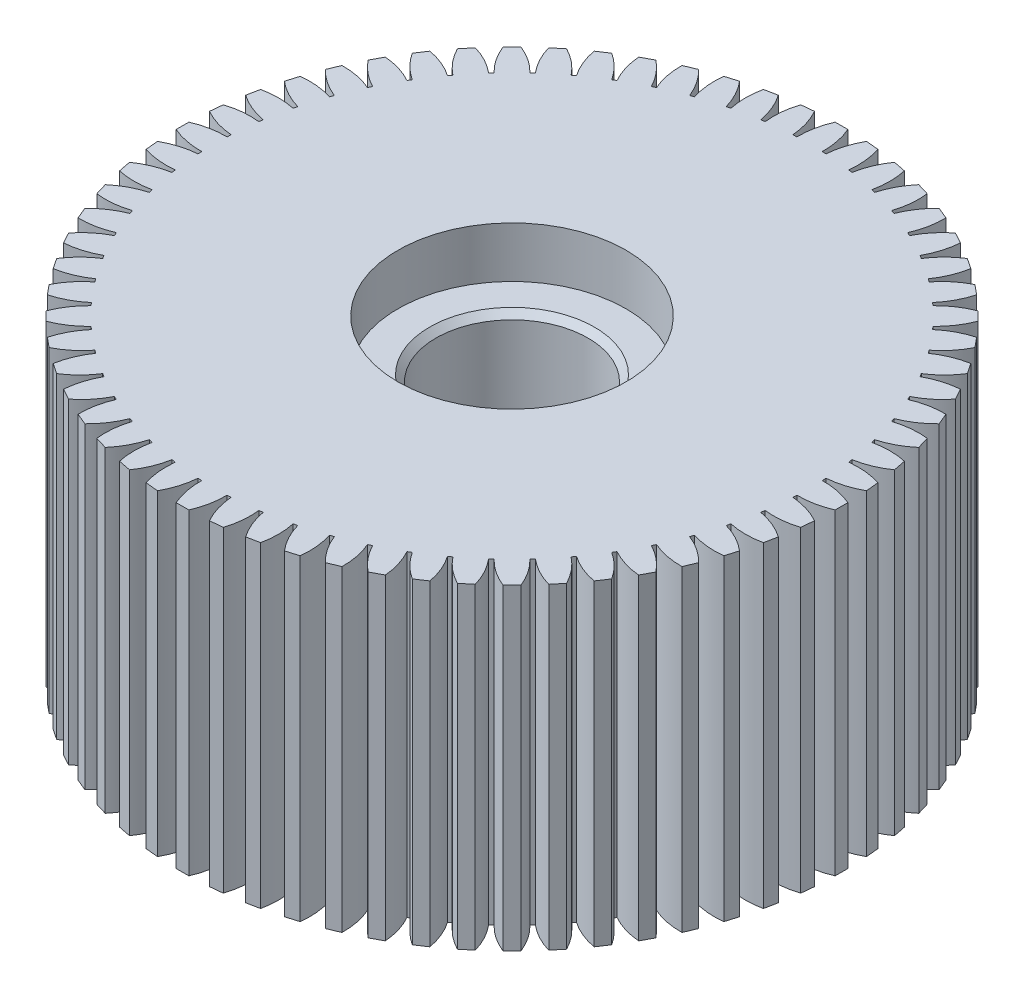
SolidWorks part; units mm, degrees
ref_plane "Front Plane" through (0, 0, 0) normal (0, 0, 1) x (1, 0, 0)
ref_plane "Top Plane" through (0, 0, 0) normal (0, 1, 0) x (1, 0, 0)
ref_plane "Right Plane" through (0, 0, 0) normal (1, 0, 0) x (0, 0, -1)
sketch "Sketch2" plane through (0, 0, 0) normal (0, 1, 0) x (1, 0, 0)
  circle A0 centre (0, 0) radius 23.5
  dimension "D1" = 47
extrude "Boss-Extrude1" add sketch "Sketch2" along normal blind 25
sketch "Sketch3" plane through (0, 25, 0) normal (0, 1, 0) x (1, 0, 0)
  line L0 (0, 0) -> (0, 28.1203) construction
  line L1 (-0.5, 25.9952) -> (0.5, 25.9952)
  line L2 (2.0504, 25.919) -> (3.0456, 25.821)
  line L3 (4.581, 25.5932) -> (5.5618, 25.3982)
  line L4 (7.0675, 25.021) -> (8.0245, 24.7307)
  line L5 (9.486, 24.2078) -> (10.4099, 23.8251)
  line L6 (11.8131, 23.1614) -> (12.695, 22.69)
  line L7 (14.0264, 21.892) -> (14.8579, 21.3364)
  line L8 (16.1047, 20.4118) -> (16.8777, 19.7774)
  line L9 (18.0278, 18.7349) -> (18.7349, 18.0278)
  line L10 (19.7774, 16.8777) -> (20.4118, 16.1047)
  line L11 (21.3364, 14.8579) -> (21.892, 14.0264)
  line L12 (22.69, 12.695) -> (23.1614, 11.8131)
  line L13 (23.8251, 10.4099) -> (24.2078, 9.486)
  line L14 (24.7307, 8.0245) -> (25.021, 7.0675)
  line L15 (25.3982, 5.5618) -> (25.5932, 4.581)
  line L16 (25.821, 3.0456) -> (25.919, 2.0504)
  line L17 (25.9952, 0.5) -> (25.9952, -0.5)
  line L18 (25.919, -2.0504) -> (25.821, -3.0456)
  line L19 (25.5932, -4.581) -> (25.3982, -5.5618)
  line L20 (25.021, -7.0675) -> (24.7307, -8.0245)
  line L21 (24.2078, -9.486) -> (23.8251, -10.4099)
  line L22 (23.1614, -11.8131) -> (22.69, -12.695)
  line L23 (21.892, -14.0264) -> (21.3364, -14.8579)
  line L24 (20.4118, -16.1047) -> (19.7774, -16.8777)
  line L25 (18.7349, -18.0278) -> (18.0278, -18.7349)
  line L26 (16.8777, -19.7774) -> (16.1047, -20.4118)
  line L27 (14.8579, -21.3364) -> (14.0264, -21.892)
  line L28 (12.695, -22.69) -> (11.8131, -23.1614)
  line L29 (10.4099, -23.8251) -> (9.486, -24.2078)
  line L30 (8.0245, -24.7307) -> (7.0675, -25.021)
  line L31 (5.5618, -25.3982) -> (4.581, -25.5932)
  line L32 (3.0456, -25.821) -> (2.0504, -25.919)
  line L33 (0.5, -25.9952) -> (-0.5, -25.9952)
  line L34 (-2.0504, -25.919) -> (-3.0456, -25.821)
  line L35 (-4.581, -25.5932) -> (-5.5618, -25.3982)
  line L36 (-7.0675, -25.021) -> (-8.0245, -24.7307)
  line L37 (-9.486, -24.2078) -> (-10.4099, -23.8251)
  line L38 (-11.8131, -23.1614) -> (-12.695, -22.69)
  line L39 (-14.0264, -21.892) -> (-14.8579, -21.3364)
  line L40 (-16.1047, -20.4118) -> (-16.8777, -19.7774)
  line L41 (-18.0278, -18.7349) -> (-18.7349, -18.0278)
  line L42 (-19.7774, -16.8777) -> (-20.4118, -16.1047)
  line L43 (-21.3364, -14.8579) -> (-21.892, -14.0264)
  line L44 (-22.69, -12.695) -> (-23.1614, -11.8131)
  line L45 (-23.8251, -10.4099) -> (-24.2078, -9.486)
  line L46 (-24.7307, -8.0245) -> (-25.021, -7.0675)
  line L47 (-25.3982, -5.5618) -> (-25.5932, -4.581)
  line L48 (-25.821, -3.0456) -> (-25.919, -2.0504)
  line L49 (-25.9952, -0.5) -> (-25.9952, 0.5)
  line L50 (-25.919, 2.0504) -> (-25.821, 3.0456)
  line L51 (-25.5932, 4.581) -> (-25.3982, 5.5618)
  line L52 (-25.021, 7.0675) -> (-24.7307, 8.0245)
  line L53 (-24.2078, 9.486) -> (-23.8251, 10.4099)
  line L54 (-23.1614, 11.8131) -> (-22.69, 12.695)
  line L55 (-21.892, 14.0264) -> (-21.3364, 14.8579)
  line L56 (-20.4118, 16.1047) -> (-19.7774, 16.8777)
  line L57 (-18.7349, 18.0278) -> (-18.0278, 18.7349)
  line L58 (-16.8777, 19.7774) -> (-16.1047, 20.4118)
  line L59 (-14.8579, 21.3364) -> (-14.0264, 21.892)
  line L60 (-12.695, 22.69) -> (-11.8131, 23.1614)
  line L61 (-10.4099, 23.8251) -> (-9.486, 24.2078)
  line L62 (-8.0245, 24.7307) -> (-7.0675, 25.021)
  line L63 (-5.5618, 25.3982) -> (-4.581, 25.5932)
  line L64 (-3.0456, 25.821) -> (-2.0504, 25.919)
  circle A0 centre (0, 0) radius 26
  circle A1 centre (0, 0) radius 23.5 construction
  circle A2 centre (0, 0) radius 23.5
  arc A3 (-1, 23.4787) -> (-0.5, 25.9952) centre (4.9989, 23.5947) cw
  arc A4 (1, 23.4787) -> (0.5, 25.9952) centre (-4.9989, 23.5947) ccw
  arc A5 (1.3061, 23.4637) -> (2.0504, 25.919) centre (7.2875, 22.9911) cw
  arc A6 (3.2965, 23.2676) -> (3.0456, 25.821) centre (-2.6621, 23.9711) ccw
  arc A7 (3.5997, 23.2227) -> (4.581, 25.5932) centre (9.5059, 22.1661) cw
  arc A8 (5.5613, 22.8325) -> (5.5618, 25.3982) centre (-0.2997, 24.1166) ccw
  arc A9 (5.8586, 22.758) -> (7.0675, 25.021) centre (11.6328, 21.1276) cw
  arc A10 (7.7725, 22.1774) -> (8.0245, 24.7307) centre (2.0656, 24.0298) ccw
  arc A11 (8.061, 22.0742) -> (9.486, 24.2078) centre (13.6477, 19.8857) cw
  arc A12 (9.9088, 21.3088) -> (10.4099, 23.8251) centre (4.4109, 23.7117) ccw
  arc A13 (10.1859, 21.1778) -> (11.8131, 23.1614) centre (15.5311, 18.4522) cw
  arc A14 (11.9497, 20.235) -> (12.695, 22.69) centre (6.7138, 23.1651) ccw
  arc A15 (12.2126, 20.0774) -> (14.0264, 21.892) centre (17.2649, 16.8411) cw
  arc A16 (13.8755, 18.9663) -> (14.8579, 21.3364) centre (8.9521, 22.3955) ccw
  arc A17 (14.1217, 18.7837) -> (16.1047, 20.4118) centre (18.8325, 15.0677) cw
  arc A18 (15.6677, 17.5149) -> (16.8777, 19.7774) centre (11.1041, 21.4102) ccw
  arc A19 (15.8949, 17.3091) -> (18.0278, 18.7349) centre (20.2187, 13.1492) cw
  arc A20 (17.3091, 15.8949) -> (18.7349, 18.0278) centre (13.1492, 20.2187) ccw
  arc A21 (17.5149, 15.6677) -> (19.7774, 16.8777) centre (21.4102, 11.1041) cw
  arc A22 (18.7837, 14.1217) -> (20.4118, 16.1047) centre (15.0677, 18.8325) ccw
  arc A23 (18.9663, 13.8755) -> (21.3364, 14.8579) centre (22.3955, 8.9521) cw
  arc A24 (20.0774, 12.2126) -> (21.892, 14.0264) centre (16.8411, 17.2649) ccw
  arc A25 (20.235, 11.9497) -> (22.69, 12.695) centre (23.1651, 6.7138) cw
  arc A26 (21.1778, 10.1859) -> (23.1614, 11.8131) centre (18.4522, 15.5311) ccw
  arc A27 (21.3088, 9.9088) -> (23.8251, 10.4099) centre (23.7117, 4.4109) cw
  arc A28 (22.0742, 8.061) -> (24.2078, 9.486) centre (19.8857, 13.6477) ccw
  arc A29 (22.1774, 7.7725) -> (24.7307, 8.0245) centre (24.0298, 2.0656) cw
  arc A30 (22.758, 5.8586) -> (25.021, 7.0675) centre (21.1276, 11.6328) ccw
  arc A31 (22.8325, 5.5613) -> (25.3982, 5.5618) centre (24.1166, -0.2997) cw
  arc A32 (23.2227, 3.5997) -> (25.5932, 4.581) centre (22.1661, 9.5059) ccw
  arc A33 (23.2676, 3.2965) -> (25.821, 3.0456) centre (23.9711, -2.6621) cw
  arc A34 (23.4637, 1.3061) -> (25.919, 2.0504) centre (22.9911, 7.2875) ccw
  arc A35 (23.4787, 1) -> (25.9952, 0.5) centre (23.5947, -4.9989) cw
  arc A36 (23.4787, -1) -> (25.9952, -0.5) centre (23.5947, 4.9989) ccw
  arc A37 (23.4637, -1.3061) -> (25.919, -2.0504) centre (22.9911, -7.2875) cw
  arc A38 (23.2676, -3.2965) -> (25.821, -3.0456) centre (23.9711, 2.6621) ccw
  arc A39 (23.2227, -3.5997) -> (25.5932, -4.581) centre (22.1661, -9.5059) cw
  arc A40 (22.8325, -5.5613) -> (25.3982, -5.5618) centre (24.1166, 0.2997) ccw
  arc A41 (22.758, -5.8586) -> (25.021, -7.0675) centre (21.1276, -11.6328) cw
  arc A42 (22.1774, -7.7725) -> (24.7307, -8.0245) centre (24.0298, -2.0656) ccw
  arc A43 (22.0742, -8.061) -> (24.2078, -9.486) centre (19.8857, -13.6477) cw
  arc A44 (21.3088, -9.9088) -> (23.8251, -10.4099) centre (23.7117, -4.4109) ccw
  arc A45 (21.1778, -10.1859) -> (23.1614, -11.8131) centre (18.4522, -15.5311) cw
  arc A46 (20.235, -11.9497) -> (22.69, -12.695) centre (23.1651, -6.7138) ccw
  arc A47 (20.0774, -12.2126) -> (21.892, -14.0264) centre (16.8411, -17.2649) cw
  arc A48 (18.9663, -13.8755) -> (21.3364, -14.8579) centre (22.3955, -8.9521) ccw
  arc A49 (18.7837, -14.1217) -> (20.4118, -16.1047) centre (15.0677, -18.8325) cw
  arc A50 (17.5149, -15.6677) -> (19.7774, -16.8777) centre (21.4102, -11.1041) ccw
  arc A51 (17.3091, -15.8949) -> (18.7349, -18.0278) centre (13.1492, -20.2187) cw
  arc A52 (15.8949, -17.3091) -> (18.0278, -18.7349) centre (20.2187, -13.1492) ccw
  arc A53 (15.6677, -17.5149) -> (16.8777, -19.7774) centre (11.1041, -21.4102) cw
  arc A54 (14.1217, -18.7837) -> (16.1047, -20.4118) centre (18.8325, -15.0677) ccw
  arc A55 (13.8755, -18.9663) -> (14.8579, -21.3364) centre (8.9521, -22.3955) cw
  arc A56 (12.2126, -20.0774) -> (14.0264, -21.892) centre (17.2649, -16.8411) ccw
  arc A57 (11.9497, -20.235) -> (12.695, -22.69) centre (6.7138, -23.1651) cw
  arc A58 (10.1859, -21.1778) -> (11.8131, -23.1614) centre (15.5311, -18.4522) ccw
  arc A59 (9.9088, -21.3088) -> (10.4099, -23.8251) centre (4.4109, -23.7117) cw
  arc A60 (8.061, -22.0742) -> (9.486, -24.2078) centre (13.6477, -19.8857) ccw
  arc A61 (7.7725, -22.1774) -> (8.0245, -24.7307) centre (2.0656, -24.0298) cw
  arc A62 (5.8586, -22.758) -> (7.0675, -25.021) centre (11.6328, -21.1276) ccw
  arc A63 (5.5613, -22.8325) -> (5.5618, -25.3982) centre (-0.2997, -24.1166) cw
  arc A64 (3.5997, -23.2227) -> (4.581, -25.5932) centre (9.5059, -22.1661) ccw
  arc A65 (3.2965, -23.2676) -> (3.0456, -25.821) centre (-2.6621, -23.9711) cw
  arc A66 (1.3061, -23.4637) -> (2.0504, -25.919) centre (7.2875, -22.9911) ccw
  arc A67 (1, -23.4787) -> (0.5, -25.9952) centre (-4.9989, -23.5947) cw
  arc A68 (-1, -23.4787) -> (-0.5, -25.9952) centre (4.9989, -23.5947) ccw
  arc A69 (-1.3061, -23.4637) -> (-2.0504, -25.919) centre (-7.2875, -22.9911) cw
  arc A70 (-3.2965, -23.2676) -> (-3.0456, -25.821) centre (2.6621, -23.9711) ccw
  arc A71 (-3.5997, -23.2227) -> (-4.581, -25.5932) centre (-9.5059, -22.1661) cw
  arc A72 (-5.5613, -22.8325) -> (-5.5618, -25.3982) centre (0.2997, -24.1166) ccw
  arc A73 (-5.8586, -22.758) -> (-7.0675, -25.021) centre (-11.6328, -21.1276) cw
  arc A74 (-7.7725, -22.1774) -> (-8.0245, -24.7307) centre (-2.0656, -24.0298) ccw
  arc A75 (-8.061, -22.0742) -> (-9.486, -24.2078) centre (-13.6477, -19.8857) cw
  arc A76 (-9.9088, -21.3088) -> (-10.4099, -23.8251) centre (-4.4109, -23.7117) ccw
  arc A77 (-10.1859, -21.1778) -> (-11.8131, -23.1614) centre (-15.5311, -18.4522) cw
  arc A78 (-11.9497, -20.235) -> (-12.695, -22.69) centre (-6.7138, -23.1651) ccw
  arc A79 (-12.2126, -20.0774) -> (-14.0264, -21.892) centre (-17.2649, -16.8411) cw
  arc A80 (-13.8755, -18.9663) -> (-14.8579, -21.3364) centre (-8.9521, -22.3955) ccw
  arc A81 (-14.1217, -18.7837) -> (-16.1047, -20.4118) centre (-18.8325, -15.0677) cw
  arc A82 (-15.6677, -17.5149) -> (-16.8777, -19.7774) centre (-11.1041, -21.4102) ccw
  arc A83 (-15.8949, -17.3091) -> (-18.0278, -18.7349) centre (-20.2187, -13.1492) cw
  arc A84 (-17.3091, -15.8949) -> (-18.7349, -18.0278) centre (-13.1492, -20.2187) ccw
  arc A85 (-17.5149, -15.6677) -> (-19.7774, -16.8777) centre (-21.4102, -11.1041) cw
  arc A86 (-18.7837, -14.1217) -> (-20.4118, -16.1047) centre (-15.0677, -18.8325) ccw
  arc A87 (-18.9663, -13.8755) -> (-21.3364, -14.8579) centre (-22.3955, -8.9521) cw
  arc A88 (-20.0774, -12.2126) -> (-21.892, -14.0264) centre (-16.8411, -17.2649) ccw
  arc A89 (-20.235, -11.9497) -> (-22.69, -12.695) centre (-23.1651, -6.7138) cw
  arc A90 (-21.1778, -10.1859) -> (-23.1614, -11.8131) centre (-18.4522, -15.5311) ccw
  arc A91 (-21.3088, -9.9088) -> (-23.8251, -10.4099) centre (-23.7117, -4.4109) cw
  arc A92 (-22.0742, -8.061) -> (-24.2078, -9.486) centre (-19.8857, -13.6477) ccw
  arc A93 (-22.1774, -7.7725) -> (-24.7307, -8.0245) centre (-24.0298, -2.0656) cw
  arc A94 (-22.758, -5.8586) -> (-25.021, -7.0675) centre (-21.1276, -11.6328) ccw
  arc A95 (-22.8325, -5.5613) -> (-25.3982, -5.5618) centre (-24.1166, 0.2997) cw
  arc A96 (-23.2227, -3.5997) -> (-25.5932, -4.581) centre (-22.1661, -9.5059) ccw
  arc A97 (-23.2676, -3.2965) -> (-25.821, -3.0456) centre (-23.9711, 2.6621) cw
  arc A98 (-23.4637, -1.3061) -> (-25.919, -2.0504) centre (-22.9911, -7.2875) ccw
  arc A99 (-23.4787, -1) -> (-25.9952, -0.5) centre (-23.5947, 4.9989) cw
  arc A100 (-23.4787, 1) -> (-25.9952, 0.5) centre (-23.5947, -4.9989) ccw
  arc A101 (-23.4637, 1.3061) -> (-25.919, 2.0504) centre (-22.9911, 7.2875) cw
  arc A102 (-23.2676, 3.2965) -> (-25.821, 3.0456) centre (-23.9711, -2.6621) ccw
  arc A103 (-23.2227, 3.5997) -> (-25.5932, 4.581) centre (-22.1661, 9.5059) cw
  arc A104 (-22.8325, 5.5613) -> (-25.3982, 5.5618) centre (-24.1166, -0.2997) ccw
  arc A105 (-22.758, 5.8586) -> (-25.021, 7.0675) centre (-21.1276, 11.6328) cw
  arc A106 (-22.1774, 7.7725) -> (-24.7307, 8.0245) centre (-24.0298, 2.0656) ccw
  arc A107 (-22.0742, 8.061) -> (-24.2078, 9.486) centre (-19.8857, 13.6477) cw
  arc A108 (-21.3088, 9.9088) -> (-23.8251, 10.4099) centre (-23.7117, 4.4109) ccw
  arc A109 (-21.1778, 10.1859) -> (-23.1614, 11.8131) centre (-18.4522, 15.5311) cw
  arc A110 (-20.235, 11.9497) -> (-22.69, 12.695) centre (-23.1651, 6.7138) ccw
  arc A111 (-20.0774, 12.2126) -> (-21.892, 14.0264) centre (-16.8411, 17.2649) cw
  arc A112 (-18.9663, 13.8755) -> (-21.3364, 14.8579) centre (-22.3955, 8.9521) ccw
  arc A113 (-18.7837, 14.1217) -> (-20.4118, 16.1047) centre (-15.0677, 18.8325) cw
  arc A114 (-17.5149, 15.6677) -> (-19.7774, 16.8777) centre (-21.4102, 11.1041) ccw
  arc A115 (-17.3091, 15.8949) -> (-18.7349, 18.0278) centre (-13.1492, 20.2187) cw
  arc A116 (-15.8949, 17.3091) -> (-18.0278, 18.7349) centre (-20.2187, 13.1492) ccw
  arc A117 (-15.6677, 17.5149) -> (-16.8777, 19.7774) centre (-11.1041, 21.4102) cw
  arc A118 (-14.1217, 18.7837) -> (-16.1047, 20.4118) centre (-18.8325, 15.0677) ccw
  arc A119 (-13.8755, 18.9663) -> (-14.8579, 21.3364) centre (-8.9521, 22.3955) cw
  arc A120 (-12.2126, 20.0774) -> (-14.0264, 21.892) centre (-17.2649, 16.8411) ccw
  arc A121 (-11.9497, 20.235) -> (-12.695, 22.69) centre (-6.7138, 23.1651) cw
  arc A122 (-10.1859, 21.1778) -> (-11.8131, 23.1614) centre (-15.5311, 18.4522) ccw
  arc A123 (-9.9088, 21.3088) -> (-10.4099, 23.8251) centre (-4.4109, 23.7117) cw
  arc A124 (-8.061, 22.0742) -> (-9.486, 24.2078) centre (-13.6477, 19.8857) ccw
  arc A125 (-7.7725, 22.1774) -> (-8.0245, 24.7307) centre (-2.0656, 24.0298) cw
  arc A126 (-5.8586, 22.758) -> (-7.0675, 25.021) centre (-11.6328, 21.1276) ccw
  arc A127 (-5.5613, 22.8325) -> (-5.5618, 25.3982) centre (0.2997, 24.1166) cw
  arc A128 (-3.5997, 23.2227) -> (-4.581, 25.5932) centre (-9.5059, 22.1661) ccw
  arc A129 (-3.2965, 23.2676) -> (-3.0456, 25.821) centre (2.6621, 23.9711) cw
  arc A130 (-1.3061, 23.4637) -> (-2.0504, 25.919) centre (-7.2875, 22.9911) ccw
  point P394 (0, 0)
  circle M4 centre (0, 0) radius 23.5
  dimension "D1" = 52
  dimension "D4" = 6
  dimension "D2" = 1
  dimension "D3" = 0.5
  dimension "D5" = 64
extrude "Boss-Extrude2" add sketch "Sketch3" against normal blind 25 contours A2 A122 L60 A121 | A2 A124 L61 A123 | A2 A120 L59 A119 | A2 A118 L58 A117 | A2 A116 L57 A115 | A2 A114 L56 A113 | A2 A112 L55 A111 | A2 A110 L54 A109 | A2 A108 L53 A107 | A2 A106 L52 A105 | A2 A104 L51 A103 | A2 A102 L50 A101 | A2 A100 L49 A99 | A2 A98 L48 A97 | A2 A96 L47 A95 | A2 A94 L46 A93 | A2 A92 L45 A91 | A2 A90 L44 A89 | A2 A88 L43 A87 | A2 A86 L42 A85 | A2 A84 L41 A83 | A2 A82 L40 A81 | A2 A80 L39 A79 | A2 A78 L38 A77 | A2 A76 L37 A75 | A2 A74 L36 A73 | A2 A72 L35 A71 | A2 A70 L34 A69 | A2 A68 L33 A67 | A2 A66 L32 A65 | A2 A64 L31 A63 | A2 A62 L30 A61 | A2 A60 L29 A59 | A2 A58 L28 A57 | A2 A56 L27 A55 | A2 A54 L26 A53 | A2 A52 L25 A51 | A2 A50 L24 A49 | A2 A48 L23 A47 | A2 A46 L22 A45 | A2 A26 L12 A25 | A2 A28 L13 A27 | A2 A30 L14 A29 | A2 A32 L15 A31 | A2 A34 L16 A33 | A2 A36 L17 A35 | A2 A38 L18 A37 | A2 A40 L19 A39 | A2 A24 L11 A23 | A2 A22 L10 A21 | A2 A20 L9 A19 | A2 A18 L8 A17 | A2 A16 L7 A15 | A2 A44 L21 A43 | A2 A42 L20 A41 | A2 A126 L62 A125 | A2 A128 L63 A127 | A2 A130 L64 A129 | L0 L1 A3 M4 | L0 A2 A4 L1 | A2 A6 L2 A5 | A2 A8 L3 A7 | A2 A10 L4 A9 | A2 A12 L5 A11 | A2 A14 L6 A13
sketch "Sketch4" plane through (0, 25, 0) normal (0, 1, 0) x (1, 0, 0)
  circle A0 centre (0, 0) radius 9
  dimension "D1" = 18
extrude "Cut-Extrude1" cut sketch "Sketch4" against normal blind 4
sketch "Sketch5" plane through (0, 25, 0) normal (0, 1, 0) x (1, 0, 0)
  circle A0 centre (0, 0) radius 6
  dimension "D1" = 12
extrude "Cut-Extrude2" cut sketch "Sketch5" against normal blind 30
chamfer "Chamfer2" distance 0.5 angle 45 1 edges at (0, 21, 6)
chamfer "Chamfer3" distance 0.5 angle 45 1 edges at (0, 0, 6)
